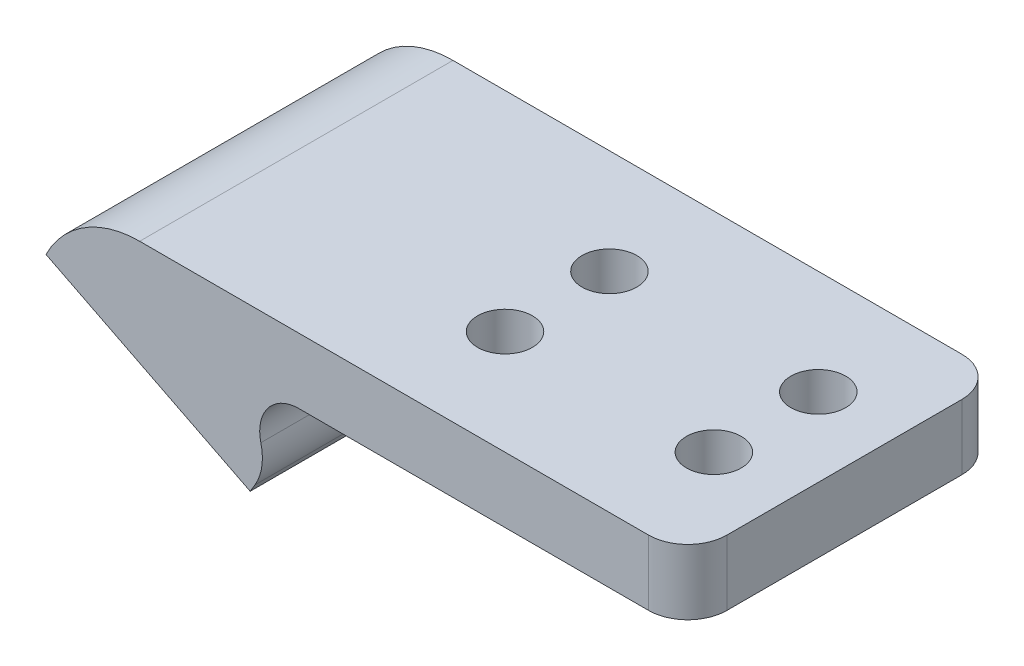
SolidWorks part; units mm, degrees
ref_plane "Plan de face" through (0, 0, 0) normal (0, 0, 1) x (1, 0, 0)
ref_plane "Plan de dessus" through (0, 0, 0) normal (0, 1, 0) x (1, 0, 0)
ref_plane "Plan de droite" through (0, 0, 0) normal (1, 0, 0) x (0, 0, -1)
sketch "Esquisse1" plane through (0, 0, 0) normal (0, 0, 1) x (1, 0, 0)
  line L1 (-6.5596, 0) -> (10.4404, 0)
  line L2 (-6.5596, 0) -> (-6.5596, 5)
  line L3 (-6.5596, 5) -> (10.4404, 5)
  line L4 (10.4404, 0) -> (10.4404, 5)
  dimension "D1" = 5
  dimension "D2" = 17
extrude "Boss.-Extru.1" add sketch "Esquisse1" along normal blind 24
sketch "Esquisse2" plane through (0, 0, 24) normal (0, 0, 1) x (1, 0, 0)
  line L0 (-6.5596, 5) -> (-16.4711, 5)
  line L1 (-16.4711, 5) -> (-0.5016, -3.0561)
  line L2 (-16.4711, 5) -> (-18.7231, 0.5359)
  line L3 (-18.7231, 0.5359) -> (-3.0805, -7.3553)
  line L4 (-3.0805, -7.3553) -> (-0.5016, -3.0561)
  line L5 (-6.5596, 5) -> (-6.5596, 0) construction
  line M4 (-6.5596, 5) -> (-6.5596, 0)
extrude "Boss.-Extru.2" add sketch "Esquisse2" against normal blind 24 contours L3 L4 L1 L2 | L0 L1 M4
fillet "Congé1" radius 4 1 edges at (-0.5016, -3.0561, 12)
fillet "Congé2" radius 8 1 edges at (-16.4711, 5, 12)
fillet "Congé3" radius 3 1 edges at (-6.5596, 0, 12)
sketch "Esquisse3" plane through (10.4404, 0, 0) normal (1, 0, 0) x (0, 0, -1)
  line L1 (0, 0) -> (-24, 0)
  line L2 (0, 0) -> (0, 5)
  line L3 (0, 5) -> (-24, 5)
  line L4 (-24, 0) -> (-24, 5)
extrude "Boss.-Extru.3" add sketch "Esquisse3" along normal blind 20
sketch "Esquisse4" plane through (0, 5, 0) normal (0, 1, 0) x (1, 0, 0)
  line L0 (20.3965, -4) -> (12.3965, -4) construction
  line L1 (8.4404, -8) -> (24.4404, -8) construction
  line L2 (12.3965, -4) -> (12.3965, -20) construction
  line L3 (12.3965, -12) -> (30.4404, -12) construction
  line L4 (30.4404, 0) -> (30.4404, -24) construction
  line L5 (8.4404, -8) -> (8.4404, -16) construction
  line L6 (8.4404, -16) -> (24.4404, -16) construction
  line L7 (24.4404, -16) -> (24.4404, -8) construction
  circle A0 centre (12.3965, -4) radius 2.1 construction
  circle A1 centre (20.3965, -4) radius 2.1 construction
  circle A2 centre (12.3965, -20) radius 2.1 construction
  circle A3 centre (20.3965, -20) radius 2.1 construction
  circle A4 centre (12.3965, -20) radius 2.1
  circle A5 centre (8.4404, -8) radius 2.1
  circle A6 centre (24.4404, -8) radius 2.1
  circle A7 centre (8.4404, -16) radius 2.1
  circle A8 centre (24.4404, -16) radius 2.1
  point P21 (8.4404, -12)
  dimension "D4" = 4.2
  dimension "D3" = 4.2
  dimension "D1" = 8
  dimension "D2" = 16
  dimension "D5" = 8
  dimension "D6" = 16
  dimension "D7" = 6
extrude "Enlèv. mat.-Extru.1" cut sketch "Esquisse4" against normal blind 10 contours A2 | A3 | A1 | A0 | A7 | A6 | A8 | A5
fillet "Congé4" radius 3 2 edges at (30.4404, 2.5, 0) (30.4404, 2.5, 24)
sketch "Esquisse5" plane through (-3.5827, -7.102, 0) normal (-0.4504, -0.8928, 0) x (0.8928, -0.4504, 0)
  line L0 (-16.9578, 12) -> (0.5625, 12) construction
  line L1 (-16.9578, 0) -> (-16.9578, 24) construction
  line L2 (0.5625, 0) -> (0.5625, 24) construction
  line L3 (-12.1477, 8.05) -> (-12.1477, 15.95) construction
  line L4 (-16.9578, 0) -> (0.5625, 0) construction
  line L5 (-8.1977, 0) -> (-8.1977, 24) construction
  line L6 (-16.9578, 24) -> (0.5625, 24) construction
  line L7 (-12.1477, 15.95) -> (-4.2477, 15.95) construction
  line L8 (-4.2477, 15.95) -> (-4.2477, 8.05) construction
  line L9 (-4.2477, 8.05) -> (-12.1477, 8.05) construction
  circle A0 centre (-12.1477, 15.95) radius 1.58 construction
  circle A1 centre (-4.2477, 15.95) radius 1.58 construction
  circle A2 centre (-12.1477, 8.05) radius 1.58 construction
  circle A3 centre (-4.2477, 8.05) radius 1.58 construction
  circle A4 centre (-12.1477, 8.05) radius 2.25
  circle A5 centre (-12.1477, 15.95) radius 2.25
  circle A6 centre (-4.2477, 15.95) radius 2.25
  circle A7 centre (-4.2477, 8.05) radius 2.25
  point P20 (-12.1477, 12)
  point P21 (-8.1977, 8.05)
  dimension "D2" = 3.16
  dimension "D3" = 4.5
  dimension "D1" = 7.9
extrude "Enlèv. mat.-Extru.2" cut sketch "Esquisse5" against normal blind 4
